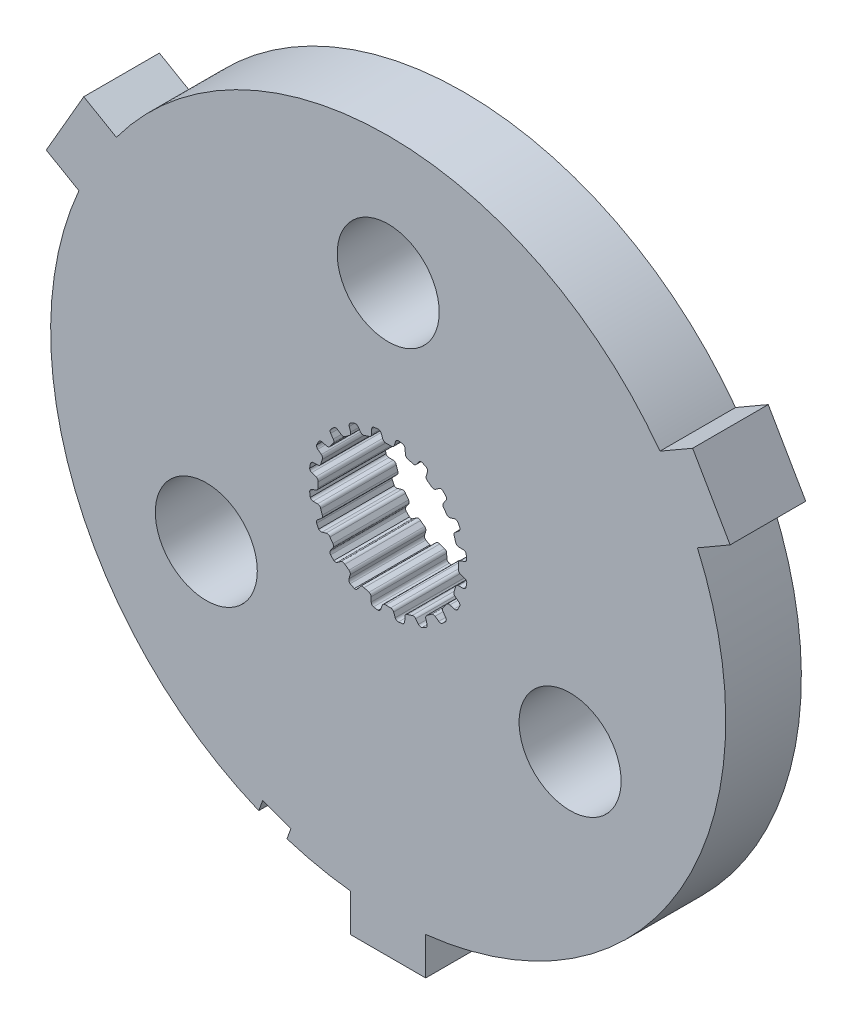
SolidWorks part; units mm, degrees
ref_plane "Front Plane" through (0, 0, 0) normal (0, 0, 1) x (1, 0, 0)
ref_plane "Top Plane" through (0, 0, 0) normal (0, 1, 0) x (1, 0, 0)
ref_plane "Right Plane" through (0, 0, 0) normal (1, 0, 0) x (0, 0, -1)
sketch "Sketch1" plane through (0, 0, 0) normal (0, 0, 1) x (1, 0, 0)
  line L0 (-0.1069, 2.9699) -> (0.1069, 2.9699)
  line L1 (0.3159, 3.2375) -> (0.2537, 3.0575)
  line L2 (-0.2964, 3.2367) -> (-0.2318, 3.0575)
  line L3 (-0.2964, 3.2367) -> (0.3159, 3.2375) construction
  line L4 (0, 3.3252) -> (0, 0) construction
  line L5 (-0.2318, 3.0575) -> (0.2537, 3.0575) construction
  line L6 (-0.4281, 3.3241) -> (0.4281, 3.3263) construction
  line L7 (0.7183, 3.1698) -> (0.7244, 2.9795)
  line L8 (0.816, 2.8576) -> (1.0195, 2.7915)
  line L9 (1.3009, 2.9815) -> (1.1862, 2.8295)
  line L10 (1.6627, 2.7927) -> (1.6097, 2.6099)
  line L11 (1.6591, 2.4655) -> (1.8322, 2.3398)
  line L12 (2.1585, 2.4335) -> (2.0025, 2.3245)
  line L13 (2.4443, 2.1423) -> (2.3374, 1.9847)
  line L14 (2.3398, 1.8322) -> (2.4655, 1.6591)
  line L15 (2.8049, 1.6474) -> (2.6228, 1.5919)
  line L16 (2.9866, 1.2821) -> (2.8363, 1.1653)
  line L17 (2.7915, 1.0195) -> (2.8576, 0.816)
  line L18 (3.1767, 0.7) -> (2.9863, 0.7035)
  line L19 (3.2367, 0.2964) -> (3.0575, 0.2318)
  line L20 (2.9699, 0.1069) -> (2.9699, -0.1069)
  line L21 (3.2375, -0.3159) -> (3.0575, -0.2537)
  line L22 (3.1698, -0.7183) -> (2.9795, -0.7244)
  line L23 (2.8576, -0.816) -> (2.7915, -1.0195)
  line L24 (2.9815, -1.3009) -> (2.8295, -1.1862)
  line L25 (2.7927, -1.6627) -> (2.6099, -1.6097)
  line L26 (2.4655, -1.6591) -> (2.3398, -1.8322)
  line L27 (2.4335, -2.1585) -> (2.3245, -2.0025)
  line L28 (2.1423, -2.4443) -> (1.9847, -2.3374)
  line L29 (1.8322, -2.3398) -> (1.6591, -2.4655)
  line L30 (1.6474, -2.8049) -> (1.5919, -2.6228)
  line L31 (1.2821, -2.9866) -> (1.1653, -2.8363)
  line L32 (1.0195, -2.7915) -> (0.816, -2.8576)
  line L33 (0.7, -3.1767) -> (0.7035, -2.9863)
  line L34 (0.2964, -3.2367) -> (0.2318, -3.0575)
  line L35 (0.1069, -2.9699) -> (-0.1069, -2.9699)
  line L36 (-0.3159, -3.2375) -> (-0.2537, -3.0575)
  line L37 (-0.7183, -3.1698) -> (-0.7244, -2.9795)
  line L38 (-0.816, -2.8576) -> (-1.0195, -2.7915)
  line L39 (-1.3009, -2.9815) -> (-1.1862, -2.8295)
  line L40 (-1.6627, -2.7927) -> (-1.6097, -2.6099)
  line L41 (-1.6591, -2.4655) -> (-1.8322, -2.3398)
  line L42 (-2.1585, -2.4335) -> (-2.0025, -2.3245)
  line L43 (-2.4443, -2.1423) -> (-2.3374, -1.9847)
  line L44 (-2.3398, -1.8322) -> (-2.4655, -1.6591)
  line L45 (-2.8049, -1.6474) -> (-2.6228, -1.5919)
  line L46 (-2.9866, -1.2821) -> (-2.8363, -1.1653)
  line L47 (-2.7915, -1.0195) -> (-2.8576, -0.816)
  line L48 (-3.1767, -0.7) -> (-2.9863, -0.7035)
  line L49 (-3.2367, -0.2964) -> (-3.0575, -0.2318)
  line L50 (-2.9699, -0.1069) -> (-2.9699, 0.1069)
  line L51 (-3.2375, 0.3159) -> (-3.0575, 0.2537)
  line L52 (-3.1698, 0.7183) -> (-2.9795, 0.7244)
  line L53 (-2.8576, 0.816) -> (-2.7915, 1.0195)
  line L54 (-2.9815, 1.3009) -> (-2.8295, 1.1862)
  line L55 (-2.7927, 1.6627) -> (-2.6099, 1.6097)
  line L56 (-2.4655, 1.6591) -> (-2.3398, 1.8322)
  line L57 (-2.4335, 2.1585) -> (-2.3245, 2.0025)
  line L58 (-2.1423, 2.4443) -> (-1.9847, 2.3374)
  line L59 (-1.8322, 2.3398) -> (-1.6591, 2.4655)
  line L60 (-1.6474, 2.8049) -> (-1.5919, 2.6228)
  line L61 (-1.2821, 2.9866) -> (-1.1653, 2.8363)
  line L62 (-1.0195, 2.7915) -> (-0.816, 2.8576)
  line L63 (-0.7, 3.1767) -> (-0.7035, 2.9863)
  line L64 (0.4281, 3.3263) -> (0.62, 3.2938)
  line L65 (1.4351, 3.0312) -> (1.6075, 2.9409)
  line L66 (2.3015, 2.4394) -> (2.4376, 2.3003)
  line L67 (2.9427, 1.6088) -> (3.0291, 1.4344)
  line L68 (3.2958, 0.6207) -> (3.3241, 0.4281)
  line L69 (3.3263, -0.4281) -> (3.2938, -0.62)
  line L70 (3.0312, -1.4351) -> (2.9409, -1.6075)
  line L71 (2.4394, -2.3015) -> (2.3003, -2.4376)
  line L72 (1.6088, -2.9427) -> (1.4344, -3.0291)
  line L73 (0.6207, -3.2958) -> (0.4281, -3.3241)
  line L74 (-0.4281, -3.3263) -> (-0.62, -3.2938)
  line L75 (-1.4351, -3.0312) -> (-1.6075, -2.9409)
  line L76 (-2.3015, -2.4394) -> (-2.4376, -2.3003)
  line L77 (-2.9427, -1.6088) -> (-3.0291, -1.4344)
  line L78 (-3.2958, -0.6207) -> (-3.3241, -0.4281)
  line L79 (-3.3263, 0.4281) -> (-3.2938, 0.62)
  line L80 (-3.0312, 1.4351) -> (-2.9409, 1.6075)
  line L81 (-2.4394, 2.3015) -> (-2.3003, 2.4376)
  line L82 (-1.6088, 2.9427) -> (-1.4344, 3.0291)
  line L83 (-0.6207, 3.2958) -> (-0.4281, 3.3241)
  arc A0 (0.2537, 3.0575) -> (0.1069, 2.9699) centre (0.1283, 3.1009) cw
  arc A1 (-0.2318, 3.0575) -> (-0.1069, 2.9699) centre (-0.1069, 3.1026) ccw
  arc A2 (0.62, 3.2938) -> (0.7183, 3.1698) centre (0.5856, 3.1656) cw
  arc A3 (0.7244, 2.9795) -> (0.816, 2.8576) centre (0.857, 2.9838) ccw
  arc A4 (-0.4281, 3.3241) -> (-0.2964, 3.2367) centre (-0.4213, 3.1916) cw
  arc A5 (0.4281, 3.3263) -> (0.3159, 3.2375) centre (0.4413, 3.1942) ccw
  arc A6 (1.1862, 2.8295) -> (1.0195, 2.7915) centre (1.0802, 2.9095) cw
  arc A7 (1.4351, 3.0312) -> (1.3009, 2.9815) centre (1.4068, 2.9015) ccw
  arc A8 (1.6075, 2.9409) -> (1.6627, 2.7927) centre (1.5352, 2.8297) cw
  arc A9 (1.6097, 2.6099) -> (1.6591, 2.4655) centre (1.7371, 2.5729) ccw
  arc A10 (2.0025, 2.3245) -> (1.8322, 2.3398) centre (1.9264, 2.4332) cw
  arc A11 (2.3015, 2.4394) -> (2.1585, 2.4335) centre (2.2346, 2.3248) ccw
  arc A12 (2.4376, 2.3003) -> (2.4443, 2.1423) centre (2.3345, 2.2168) cw
  arc A13 (2.3374, 1.9847) -> (2.3398, 1.8322) centre (2.4472, 1.9102) ccw
  arc A14 (2.6228, 1.5919) -> (2.4655, 1.6591) centre (2.5841, 1.7189) cw
  arc A15 (2.9427, 1.6088) -> (2.8049, 1.6474) centre (2.8436, 1.5205) ccw
  arc A16 (3.0291, 1.4344) -> (2.9866, 1.2821) centre (2.9052, 1.3869) cw
  arc A17 (2.8363, 1.1653) -> (2.7915, 1.0195) centre (2.9177, 1.0605) ccw
  arc A18 (2.9863, 0.7035) -> (2.8576, 0.816) centre (2.9887, 0.8362) cw
  arc A19 (3.2958, 0.6207) -> (3.1767, 0.7) centre (3.1743, 0.5673) ccw
  arc A20 (3.3241, 0.4281) -> (3.2367, 0.2964) centre (3.1916, 0.4213) cw
  arc A21 (3.0575, 0.2318) -> (2.9699, 0.1069) centre (3.1026, 0.1069) ccw
  arc A22 (3.0575, -0.2537) -> (2.9699, -0.1069) centre (3.1009, -0.1283) cw
  arc A23 (3.3263, -0.4281) -> (3.2375, -0.3159) centre (3.1942, -0.4413) ccw
  arc A24 (3.2938, -0.62) -> (3.1698, -0.7183) centre (3.1656, -0.5856) cw
  arc A25 (2.9795, -0.7244) -> (2.8576, -0.816) centre (2.9838, -0.857) ccw
  arc A26 (2.8295, -1.1862) -> (2.7915, -1.0195) centre (2.9095, -1.0802) cw
  arc A27 (3.0312, -1.4351) -> (2.9815, -1.3009) centre (2.9015, -1.4068) ccw
  arc A28 (2.9409, -1.6075) -> (2.7927, -1.6627) centre (2.8297, -1.5352) cw
  arc A29 (2.6099, -1.6097) -> (2.4655, -1.6591) centre (2.5729, -1.7371) ccw
  arc A30 (2.3245, -2.0025) -> (2.3398, -1.8322) centre (2.4332, -1.9264) cw
  arc A31 (2.4394, -2.3015) -> (2.4335, -2.1585) centre (2.3248, -2.2346) ccw
  arc A32 (2.3003, -2.4376) -> (2.1423, -2.4443) centre (2.2168, -2.3345) cw
  arc A33 (1.9847, -2.3374) -> (1.8322, -2.3398) centre (1.9102, -2.4472) ccw
  arc A34 (1.5919, -2.6228) -> (1.6591, -2.4655) centre (1.7189, -2.5841) cw
  arc A35 (1.6088, -2.9427) -> (1.6474, -2.8049) centre (1.5205, -2.8436) ccw
  arc A36 (1.4344, -3.0291) -> (1.2821, -2.9866) centre (1.3869, -2.9052) cw
  arc A37 (1.1653, -2.8363) -> (1.0195, -2.7915) centre (1.0605, -2.9177) ccw
  arc A38 (0.7035, -2.9863) -> (0.816, -2.8576) centre (0.8362, -2.9887) cw
  arc A39 (0.6207, -3.2958) -> (0.7, -3.1767) centre (0.5673, -3.1743) ccw
  arc A40 (0.4281, -3.3241) -> (0.2964, -3.2367) centre (0.4213, -3.1916) cw
  arc A41 (0.2318, -3.0575) -> (0.1069, -2.9699) centre (0.1069, -3.1026) ccw
  arc A42 (-0.2537, -3.0575) -> (-0.1069, -2.9699) centre (-0.1283, -3.1009) cw
  arc A43 (-0.4281, -3.3263) -> (-0.3159, -3.2375) centre (-0.4413, -3.1942) ccw
  arc A44 (-0.62, -3.2938) -> (-0.7183, -3.1698) centre (-0.5856, -3.1656) cw
  arc A45 (-0.7244, -2.9795) -> (-0.816, -2.8576) centre (-0.857, -2.9838) ccw
  arc A46 (-1.1862, -2.8295) -> (-1.0195, -2.7915) centre (-1.0802, -2.9095) cw
  arc A47 (-1.4351, -3.0312) -> (-1.3009, -2.9815) centre (-1.4068, -2.9015) ccw
  arc A48 (-1.6075, -2.9409) -> (-1.6627, -2.7927) centre (-1.5352, -2.8297) cw
  arc A49 (-1.6097, -2.6099) -> (-1.6591, -2.4655) centre (-1.7371, -2.5729) ccw
  arc A50 (-2.0025, -2.3245) -> (-1.8322, -2.3398) centre (-1.9264, -2.4332) cw
  arc A51 (-2.3015, -2.4394) -> (-2.1585, -2.4335) centre (-2.2346, -2.3248) ccw
  arc A52 (-2.4376, -2.3003) -> (-2.4443, -2.1423) centre (-2.3345, -2.2168) cw
  arc A53 (-2.3374, -1.9847) -> (-2.3398, -1.8322) centre (-2.4472, -1.9102) ccw
  arc A54 (-2.6228, -1.5919) -> (-2.4655, -1.6591) centre (-2.5841, -1.7189) cw
  arc A55 (-2.9427, -1.6088) -> (-2.8049, -1.6474) centre (-2.8436, -1.5205) ccw
  arc A56 (-3.0291, -1.4344) -> (-2.9866, -1.2821) centre (-2.9052, -1.3869) cw
  arc A57 (-2.8363, -1.1653) -> (-2.7915, -1.0195) centre (-2.9177, -1.0605) ccw
  arc A58 (-2.9863, -0.7035) -> (-2.8576, -0.816) centre (-2.9887, -0.8362) cw
  arc A59 (-3.2958, -0.6207) -> (-3.1767, -0.7) centre (-3.1743, -0.5673) ccw
  arc A60 (-3.3241, -0.4281) -> (-3.2367, -0.2964) centre (-3.1916, -0.4213) cw
  arc A61 (-3.0575, -0.2318) -> (-2.9699, -0.1069) centre (-3.1026, -0.1069) ccw
  arc A62 (-3.0575, 0.2537) -> (-2.9699, 0.1069) centre (-3.1009, 0.1283) cw
  arc A63 (-3.3263, 0.4281) -> (-3.2375, 0.3159) centre (-3.1942, 0.4413) ccw
  arc A64 (-3.2938, 0.62) -> (-3.1698, 0.7183) centre (-3.1656, 0.5856) cw
  arc A65 (-2.9795, 0.7244) -> (-2.8576, 0.816) centre (-2.9838, 0.857) ccw
  arc A66 (-2.8295, 1.1862) -> (-2.7915, 1.0195) centre (-2.9095, 1.0802) cw
  arc A67 (-3.0312, 1.4351) -> (-2.9815, 1.3009) centre (-2.9015, 1.4068) ccw
  arc A68 (-2.9409, 1.6075) -> (-2.7927, 1.6627) centre (-2.8297, 1.5352) cw
  arc A69 (-2.6099, 1.6097) -> (-2.4655, 1.6591) centre (-2.5729, 1.7371) ccw
  arc A70 (-2.3245, 2.0025) -> (-2.3398, 1.8322) centre (-2.4332, 1.9264) cw
  arc A71 (-2.4394, 2.3015) -> (-2.4335, 2.1585) centre (-2.3248, 2.2346) ccw
  arc A72 (-2.3003, 2.4376) -> (-2.1423, 2.4443) centre (-2.2168, 2.3345) cw
  arc A73 (-1.9847, 2.3374) -> (-1.8322, 2.3398) centre (-1.9102, 2.4472) ccw
  arc A74 (-1.5919, 2.6228) -> (-1.6591, 2.4655) centre (-1.7189, 2.5841) cw
  arc A75 (-1.6088, 2.9427) -> (-1.6474, 2.8049) centre (-1.5205, 2.8436) ccw
  arc A76 (-1.4344, 3.0291) -> (-1.2821, 2.9866) centre (-1.3869, 2.9052) cw
  arc A77 (-1.1653, 2.8363) -> (-1.0195, 2.7915) centre (-1.0605, 2.9177) ccw
  arc A78 (-0.7035, 2.9863) -> (-0.816, 2.8576) centre (-0.8362, 2.9887) cw
  arc A79 (-0.6207, 3.2958) -> (-0.7, 3.1767) centre (-0.5673, 3.1743) ccw
  circle A80 centre (0, 0) radius 14.2875
  point P14 (0, 2.9699)
  point P247 (0, 0)
  dimension "D4" = 0.1327
  dimension "D8" = 20
  dimension "D9" = 28.575
  dimension "D1" = 2.9699
  dimension "D2" = 0.2139
  dimension "D3" = 0.1904
  dimension "D5" = 0.0877
  dimension "D6" = 0.4855
  dimension "D7" = 0.8563
extrude "Boss-Extrude1" add sketch "Sketch1" along normal blind 3.2004
sketch "Sketch5" plane through (0, 0, 3.2004) normal (0, 0, 1) x (1, 0, 0)
  line L0 (0, 8.89) -> (0, 0) construction
  line L1 (0, 3.3252) -> (0, 0) construction
  circle A0 centre (0, 0) radius 14.2875 construction
  circle A1 centre (0, 8.89) radius 2.159
  circle A2 centre (7.699, -4.445) radius 2.159
  circle A3 centre (-7.699, -4.445) radius 2.159
  point P15 (0, 0)
  dimension "D2" = 4.318
  dimension "D1" = 8.89
  dimension "D3" = 3
extrude "Cut-Extrude2" cut sketch "Sketch5" against normal up to surface (3.2004 mm away) up to face at (14.2875, 0, 0)
sketch "Sketch6" plane through (0, 0, 3.2004) normal (0, 0, 1) x (1, 0, 0)
  line L0 (0, -15.7954) -> (0, 0) construction
  line L1 (0, 0) -> (13.6792, 7.8977) construction
  line L2 (0, 0) -> (-13.6792, 7.8977) construction
  line L3 (0, 8.89) -> (0, 0) construction
  line L4 (1.5875, -15.7954) -> (-1.5875, -15.7954)
  line L5 (1.5875, -15.7954) -> (1.5875, -14.199)
  line L6 (1.5875, -14.199) -> (-1.5875, -14.199) construction
  line L7 (-1.5875, -15.7954) -> (-1.5875, -14.199)
  line L8 (13.0905, 5.7247) -> (11.503, 8.4743) construction
  line L9 (13.0905, 5.7247) -> (14.473, 6.5229)
  line L10 (14.473, 6.5229) -> (12.8855, 9.2725)
  line L11 (11.503, 8.4743) -> (12.8855, 9.2725)
  line L12 (-13.0905, 5.7247) -> (-14.473, 6.5229)
  line L13 (-13.0905, 5.7247) -> (-11.503, 8.4743) construction
  line L14 (-11.503, 8.4743) -> (-12.8855, 9.2725)
  line L15 (-14.473, 6.5229) -> (-12.8855, 9.2725)
  circle A1 centre (0, 0) radius 15.875 construction
  arc A2 (1.5875, -14.199) -> (13.0905, 5.7247) centre (0, 0) ccw
  arc A3 (11.503, 8.4743) -> (-11.503, 8.4743) centre (0, 0) ccw
  arc A4 (-1.5875, -14.199) -> (-13.0905, 5.7247) centre (0, 0) cw
  circle A5 centre (0, 0) radius 14.2875 construction
  circle A6 centre (7.699, -4.445) radius 2.159
  circle A7 centre (-7.699, -4.445) radius 2.159
  circle A8 centre (0, 8.89) radius 2.159
  circle A9 centre (7.699, -4.445) radius 2.159 construction
  circle A10 centre (-7.699, -4.445) radius 2.159 construction
  circle A11 centre (0, 8.89) radius 2.159 construction
  circle A12 centre (0, 0) radius 5.9271
  point P37 (13.5764, 8.0733)
  point P38 (0.4746, -15.7883)
  dimension "D1" = 31.75
  dimension "D3" = 14.2875
  dimension "D2" = 3.175
  dimension "D4" = 120
  dimension "D5" = 120
extrude "Boss-Extrude2" add sketch "Sketch6" against normal up to surface (3.2004 mm away) up to face at (2.159, 8.89, 0)
sketch "Sketch7" plane through (0, 0, 3.2004) normal (0, 0, 1) x (1, 0, 0)
  line L0 (-4.8866, -13.4259) -> (0, 0) construction
  line L1 (-4.2899, -13.643) -> (-4.1162, -13.1657)
  line L2 (-4.1162, -13.1657) -> (-5.3096, -12.7313)
  line L3 (-5.3096, -12.7313) -> (-5.4833, -13.2087)
  line L4 (-5.4833, -13.2087) -> (-4.2899, -13.643)
  line L5 (0, -15.7954) -> (0, 0) construction
  arc A0 (-13.0905, 5.7247) -> (-1.5875, -14.199) centre (0, 0) ccw construction
  dimension "D1" = 1.27
  dimension "D2" = 0.508
  dimension "D3" = 20
extrude "Cut-Extrude3" cut sketch "Sketch7" against normal up to surface (3.2004 mm away) up to face at (2.159, 8.89, 0)
